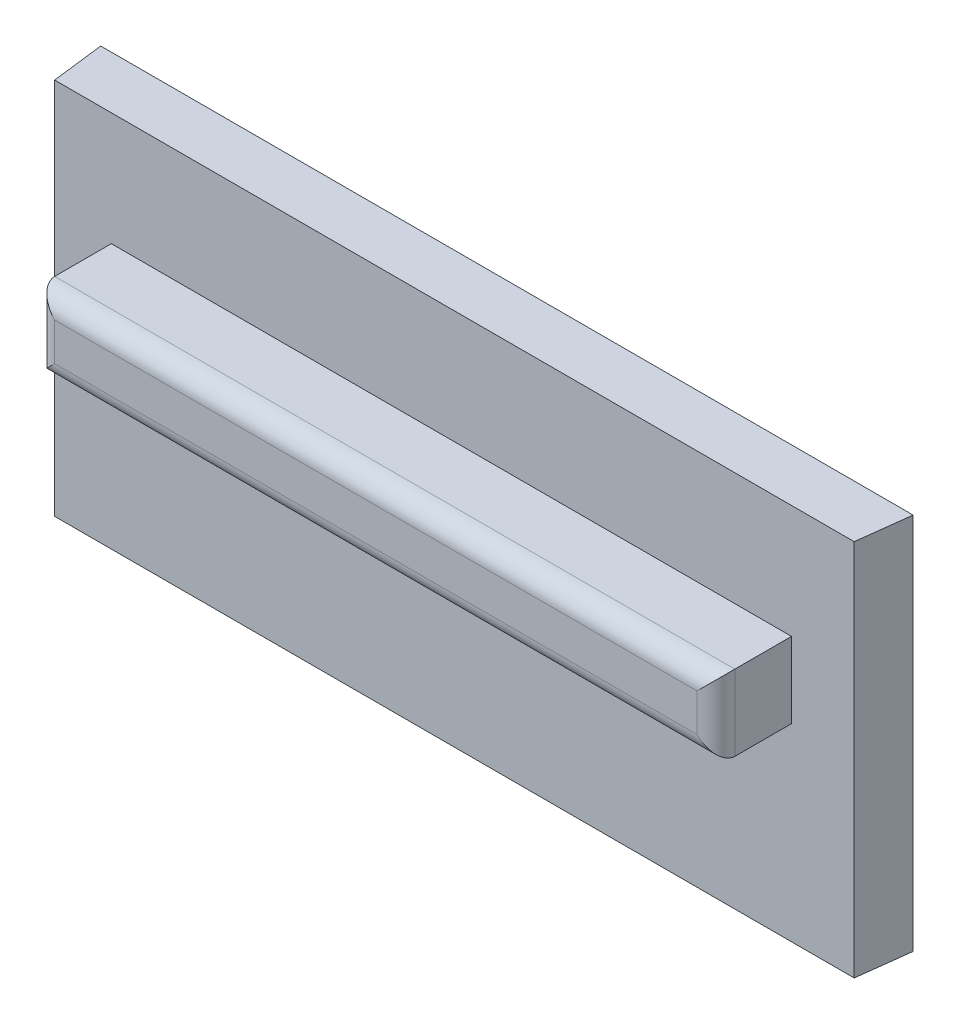
SolidWorks part; units mm, degrees
ref_plane "Plano frontal" through (0, 0, 0) normal (0, 0, 1) x (1, 0, 0)
ref_plane "Plano superior" through (0, 0, 0) normal (0, 1, 0) x (1, 0, 0)
ref_plane "Plano direito" through (0, 0, 0) normal (1, 0, 0) x (0, 0, -1)
sketch "Esboço3" plane through (0, 0, 0) normal (0, 1, 0) x (1, 0, 0)
  line L0 (0, 133.306) -> (0, -136.6576) construction
  line L1 (21.5747, 89.6947) -> (21.7453, 91.0843)
  line L2 (0.4159, 89.6947) -> (0.2453, 91.0843)
  line L3 (0.2453, 91.0843) -> (21.7453, 91.0843)
  line L4 (17.848, 93.7393) -> (16.7638, 94.9159) construction
  line L5 (0.4159, 89.6947) -> (21.5747, 89.6947)
  dimension "D1" = 1.4
  dimension "D2" = 1.4
  dimension "D3" = 21.5
extrude "Ressalto-extrusão1" add sketch "Esboço3" along normal blind 10
sketch "Esboço4" plane through (0, 0, -89.6947) normal (0, 0, 1) x (1, 0, 0)
  line L0 (0.4159, 10) -> (21.5747, 10) construction
  line L1 (1.9159, 5) -> (19.9159, 5)
  line L2 (1.9159, 5) -> (1.9159, 7)
  line L3 (1.9159, 7) -> (19.9159, 7)
  line L4 (19.9159, 5) -> (19.9159, 7)
  line L5 (0.4159, 10) -> (0.4159, 0) construction
  dimension "D1" = 3
  dimension "D2" = 2
  dimension "D3" = 18
  dimension "D4" = 1.5
extrude "Ressalto-extrusão2" add sketch "Esboço4" along normal blind 2
fillet "Filete1" radius 0.5 4 edges at (10.9159, 7, -87.6947) (19.9159, 6, -87.6947) (10.9159, 5, -87.6947) (1.9159, 6, -87.6947)
